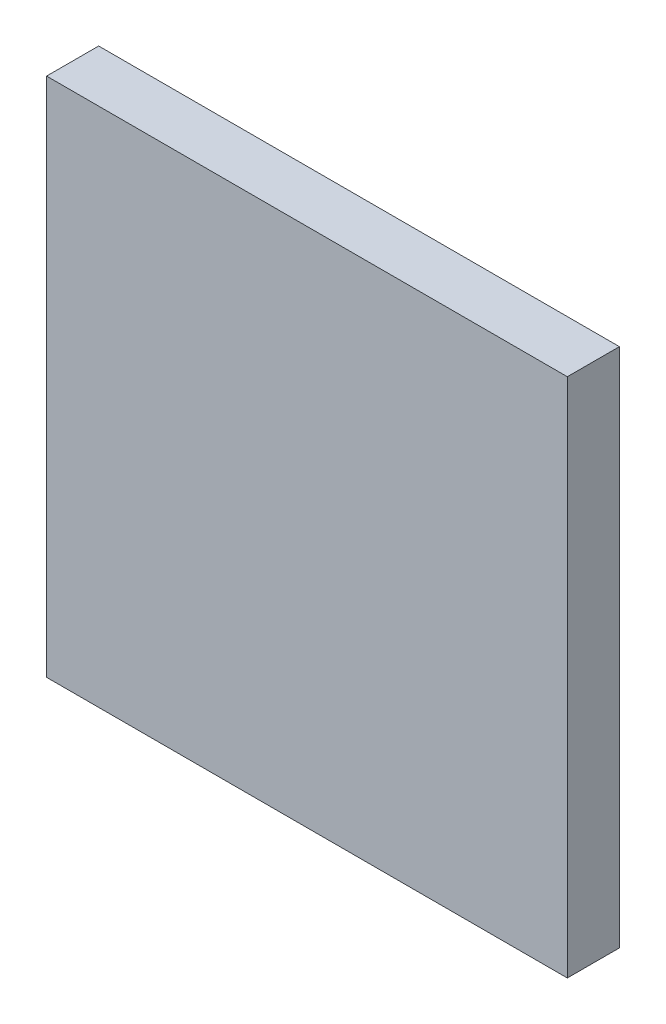
SolidWorks part; units mm, degrees
ref_plane "Front Plane" through (0, 0, 0) normal (0, 0, 1) x (1, 0, 0)
ref_plane "Top Plane" through (0, 0, 0) normal (0, 1, 0) x (1, 0, 0)
ref_plane "Right Plane" through (0, 0, 0) normal (1, 0, 0) x (0, 0, -1)
sketch "Sketch1" plane through (0, 0, 0) normal (0, 0, 1) x (1, 0, 0)
  line L1 (-2500, -2500) -> (2500, -2500)
  line L2 (-2500, -2500) -> (-2500, 2500)
  line L3 (-2500, 2500) -> (2500, 2500)
  line L4 (2500, -2500) -> (2500, 2500)
  line L5 (-2500, -2500) -> (2500, 2500) construction
  line L6 (-2500, 2500) -> (2500, -2500) construction
  point P0 (0, 0)
  dimension "D1" = 5000
  dimension "D2" = 5000
extrude "Boss-Extrude1" add sketch "Sketch1" along normal blind 500
